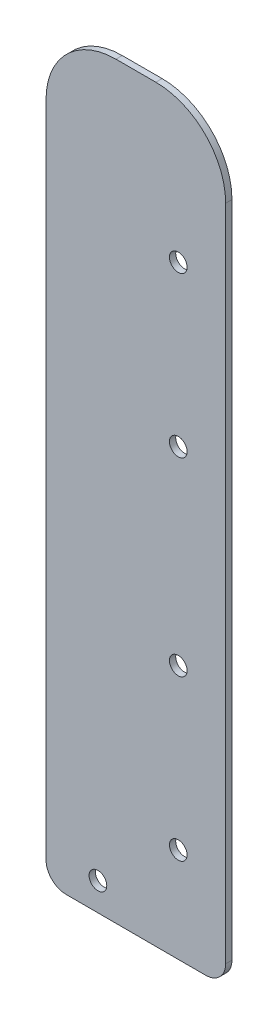
SolidWorks part; units mm, degrees
ref_plane "Front Plane" through (0, 0, 0) normal (0, 0, 1) x (1, 0, 0)
ref_plane "Top Plane" through (0, 0, 0) normal (0, 1, 0) x (1, 0, 0)
ref_plane "Right Plane" through (0, 0, 0) normal (1, 0, 0) x (0, 0, -1)
sketch "Sketch1" plane through (0, 0, 0) normal (0, 0, 1) x (1, 0, 0)
  line L1 (0, -146.6506) -> (0, 146.6506) construction
  line L3 (45.72, 5.08) -> (45.72, 172.72)
  line L5 (40.64, 0) -> (33.655, 0)
  line L7 (66.681, 0) -> (66.681, 88.9) construction
  line L8 (33.655, 0) -> (45.72, 0) construction
  line L9 (33.655, 177.8) -> (33.655, 0) construction
  line L10 (118.1346, 0) -> (-118.1346, 0) construction
  line L11 (66.681, 88.9) -> (0, 88.9) construction
  line L14 (33.655, 0) -> (5.07, 0.0545)
  line L18 (66.681, 88.9) -> (66.681, 177.8) construction
  line L19 (66.681, 177.8) -> (0, 177.8) construction
  line L20 (0, 5.08) -> (0, 172.72)
  line L23 (33.655, 0) -> (25.4, 0.0158) construction
  line L25 (25.4, 0.0158) -> (19.812, 0.0264) construction
  line L26 (19.812, 0.0264) -> (19.812, 8.89) construction
  line L27 (19.812, 8.89) -> (19.812, 177.8) construction
  line L28 (33.655, 24.13) -> (0, 24.13) construction
  line L35 (25.4, 0.0158) -> (22.7313, 0.0208) construction
  line L46 (17.78, 190.5) -> (27.94, 190.5)
  line L47 (19.9023, 177.8) -> (19.9023, 190.5) construction
  line L48 (20.4442, 160.274) -> (19.9023, 190.5) construction
  line L49 (19.9023, 190.5) -> (-14.4304, 190.5) construction
  line L50 (20.4442, 160.274) -> (0, 160.274) construction
  line L51 (45.72, 10.2129) -> (43.18, 10.2129) construction
  line L52 (43.18, 10.2129) -> (43.18, 0.6806) construction
  line L53 (43.18, 0.6806) -> (43.18, 181.8781) construction
  circle A0 centre (33.655, 24.13) radius 2.2479
  circle A1 centre (33.655, 64.77) radius 2.2479
  arc A5 (40.64, 0) -> (45.72, 5.08) centre (40.64, 5.08) ccw
  arc A6 (5.07, 0.0545) -> (0, 5.08) centre (5.0797, 5.1345) cw
  circle A7 centre (33.655, 113.03) radius 2.2479
  circle A8 centre (33.655, 153.67) radius 2.2479
  arc A13 (45.72, 172.72) -> (27.94, 190.5) centre (27.94, 172.72) ccw
  arc A14 (0, 172.72) -> (17.78, 190.5) centre (17.78, 172.72) cw
  circle A15 centre (13.208, 7.151) radius 2.2479
  point P24 (0, 190.5)
  point P30 (0, 0)
  point P38 (0, 190.5)
  point P42 (0, 185.42)
  point P46 (40.64, 185.0608)
  point P52 (0, 190.5)
  dimension "D7" = 4.4958
  dimension "D5" = 24.13
  dimension "D6" = 4.4958
  dimension "D9" = 24.13
  dimension "D11" = 88.9
  dimension "D12" = 5.08
  dimension "D13" = 4.4958
  dimension "D15" = 4.4958
  dimension "D17" = 4.4958
  dimension "D19" = 17.78
  dimension "D22" = 15.24
  dimension "D26" = 2.54
  dimension "D20" = 32.512
  dimension "D25" = 12.7
  dimension "D27" = 9.525
  dimension "D1" = 190.5
  dimension "D2" = 45.72
  dimension "D3" = 88.9
  dimension "D4" = 9.525
  dimension "D8" = 40.64
  dimension "D10" = 24.13
  dimension "D14" = 7.112
  dimension "D16" = 40.64
  dimension "D18" = 24.13
  dimension "D21" = 30.226
  dimension "D24" = 25.908
  dimension "D28" = 64.77
extrude "Boss-Extrude2" add sketch "Sketch1" along normal blind 1.6002
